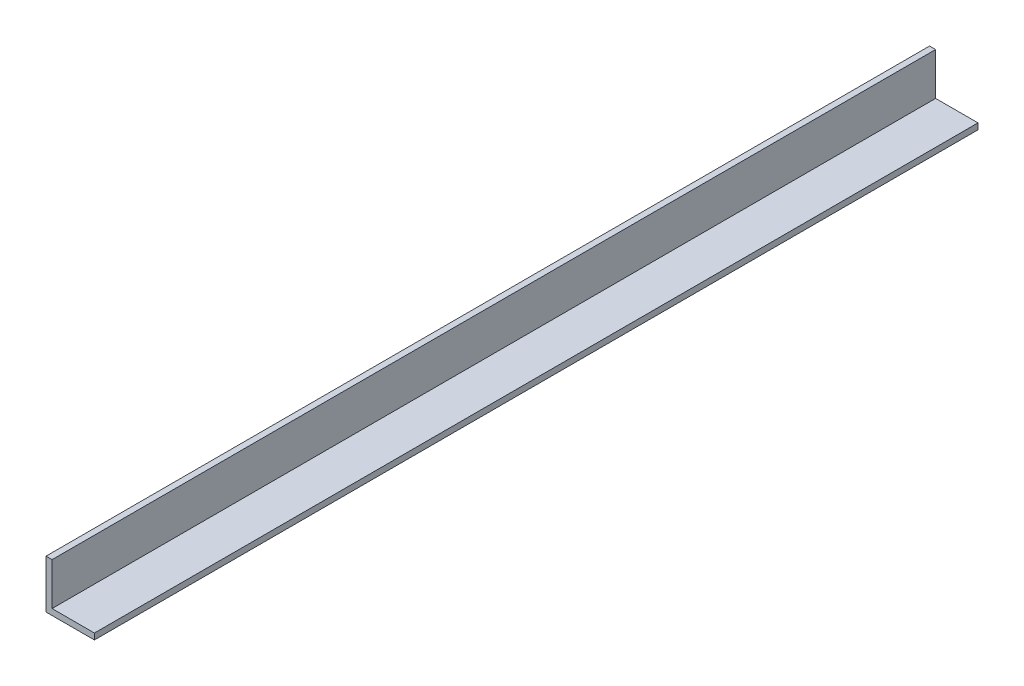
SolidWorks part; units mm, degrees
ref_plane "Front Plane" through (0, 0, 0) normal (0, 0, 1) x (1, 0, 0)
ref_plane "Top Plane" through (0, 0, 0) normal (0, 1, 0) x (1, 0, 0)
ref_plane "Right Plane" through (0, 0, 0) normal (1, 0, 0) x (0, 0, -1)
sketch "Sketch1" plane through (0, 0, 0) normal (0, 0, 1) x (1, 0, 0)
  line L1 (0, 0) -> (0, 50.8)
  line L2 (0, 0) -> (50.8, 0)
  line L3 (50.8, 0) -> (50.8, 6.35)
  line L4 (50.8, 6.35) -> (6.35, 6.35)
  line L5 (6.35, 6.35) -> (6.35, 50.8)
  line L6 (6.35, 50.8) -> (0, 50.8)
  dimension "D2" = 50.8
  dimension "D3" = 6.35
extrude "Boss-Extrude1" add sketch "Sketch1" along normal blind 927.1
